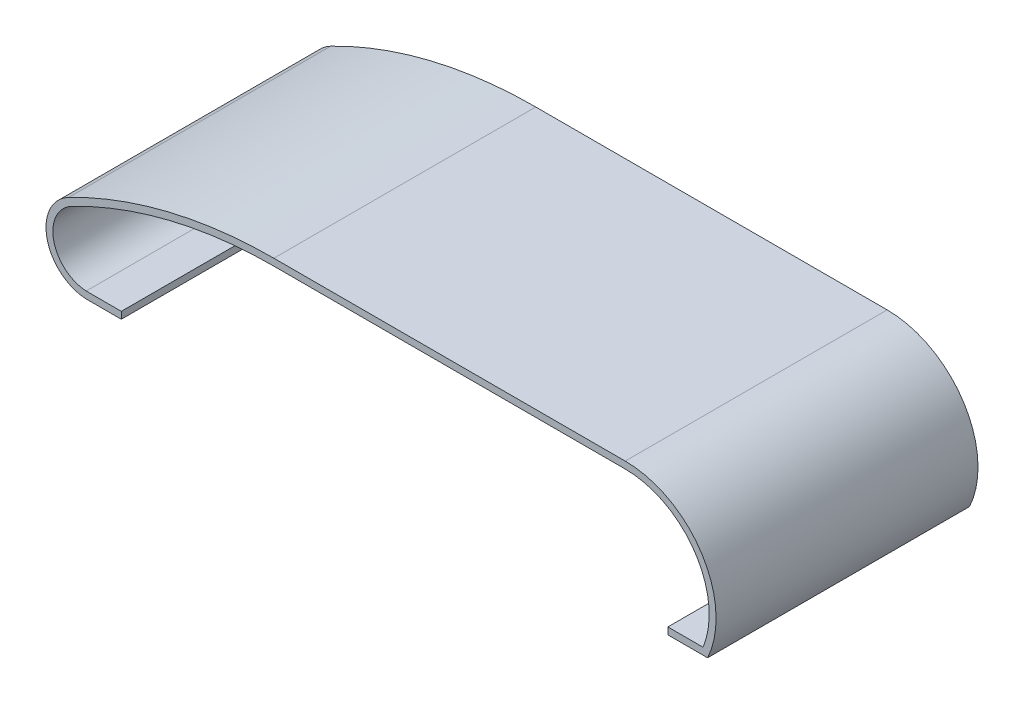
SolidWorks part; units mm, degrees
ref_plane "Front Plane" through (0, 0, 0) normal (0, 0, 1) x (1, 0, 0)
ref_plane "Top Plane" through (0, 0, 0) normal (0, 1, 0) x (1, 0, 0)
ref_plane "Right Plane" through (0, 0, 0) normal (1, 0, 0) x (0, 0, -1)
sketch "Sketch1" plane through (0, 0, 0) normal (0, 0, 1) x (1, 0, 0)
  line L1 (77.813, -3.2432) -> (72.7051, -3.2428)
  line L4 (77.813, -3.2432) -> (77.8131, -1.7432) construction
  line L5 (-11.687, -3.2364) -> (-11.6869, -1.7364) construction
  line L7 (66.52, 13.5) -> (15.54, 13.5)
  line L8 (78.4684, -4.2432) -> (72.705, -4.2428)
  line L9 (66.52, 14.5) -> (15.54, 14.5)
  line L10 (77.813, -3.2432) -> (72.7051, -3.2428)
  line L11 (72.7051, -3.2428) -> (72.705, -4.2428)
  line L12 (-11.687, -3.2364) -> (-6.5903, -3.2368)
  line L13 (-6.5903, -3.2368) -> (-6.5904, -4.2368)
  line L15 (-6.5904, -4.2368) -> (-11.7115, -4.2364)
  line L16 (-6.5903, -3.2368) -> (-11.687, -3.2364)
  line L17 (78.4684, -4.2432) -> (-11.7115, -4.2364) construction
  line L19 (77.813, -3.2432) -> (-11.687, -3.2364) construction
  arc A0 (66.52, 13.5) -> (77.813, -3.2432) centre (66.52, 1.32) cw
  arc A1 (15.54, 13.5) -> (-13.7656, 6.3686) centre (15.54, -50.2796) ccw
  arc A2 (-13.7656, 6.3686) -> (-11.687, -3.2364) centre (-11.4266, 1.8474) ccw
  arc A3 (66.52, 14.5) -> (78.4684, -4.2432) centre (66.52, 1.32) cw
  arc A4 (-14.225, 7.2568) -> (-11.7115, -4.2364) centre (-11.4266, 1.8474) ccw
  arc A5 (15.54, 14.5) -> (-14.225, 7.2568) centre (15.54, -50.2796) ccw
  dimension "D1" = 1
extrude "Boss-Extrude1" add sketch "Sketch1" along normal blind 38 contours L9 A5 A4 L15 L13 L12 A2 A1 L7 A0 L1 L11 L8 A3
sketch "Sketch2" plane through (0, 0, 0) normal (0, 0, -1) x (-1, 0, 0)
  line L0 (-72.705, -4.2428) -> (6.5904, -4.2368)
  line L8 (-15.54, 14.5) -> (-66.52, 14.5)
  line L9 (-78.4684, -4.2432) -> (-72.705, -4.2428)
  line L10 (-72.705, -4.2428) -> (-72.7051, -3.2428)
  line L11 (-72.7051, -3.2428) -> (-77.813, -3.2432)
  line L12 (-66.52, 13.5) -> (-15.54, 13.5)
  line L13 (11.687, -3.2364) -> (6.5903, -3.2368)
  line L14 (6.5903, -3.2368) -> (6.5904, -4.2368)
  line L15 (6.5904, -4.2368) -> (11.7115, -4.2364)
  line L16 (-15.54, 14.5) -> (-66.52, 14.5)
  line L17 (-78.4684, -4.2432) -> (-72.705, -4.2428)
  line L23 (6.5904, -4.2368) -> (11.7115, -4.2364)
  arc A6 (-66.52, 14.5) -> (-78.4684, -4.2432) centre (-66.52, 1.32) ccw
  arc A7 (-66.52, 13.5) -> (-77.813, -3.2432) centre (-66.52, 1.32) ccw
  arc A8 (13.7656, 6.3686) -> (-15.54, 13.5) centre (-15.54, -50.2796) ccw
  arc A9 (11.687, -3.2364) -> (13.7656, 6.3686) centre (11.4266, 1.8474) ccw
  arc A10 (11.7115, -4.2364) -> (14.225, 7.2568) centre (11.4266, 1.8474) ccw
  arc A11 (14.225, 7.2568) -> (-15.54, 14.5) centre (-15.54, -50.2796) ccw
  arc A12 (-66.52, 14.5) -> (-78.4684, -4.2432) centre (-66.52, 1.32) ccw
  arc A16 (11.7115, -4.2364) -> (14.225, 7.2568) centre (11.4266, 1.8474) ccw
  arc A17 (14.225, 7.2568) -> (-15.54, 14.5) centre (-15.54, -50.2796) ccw
  dimension "D1" = 0
